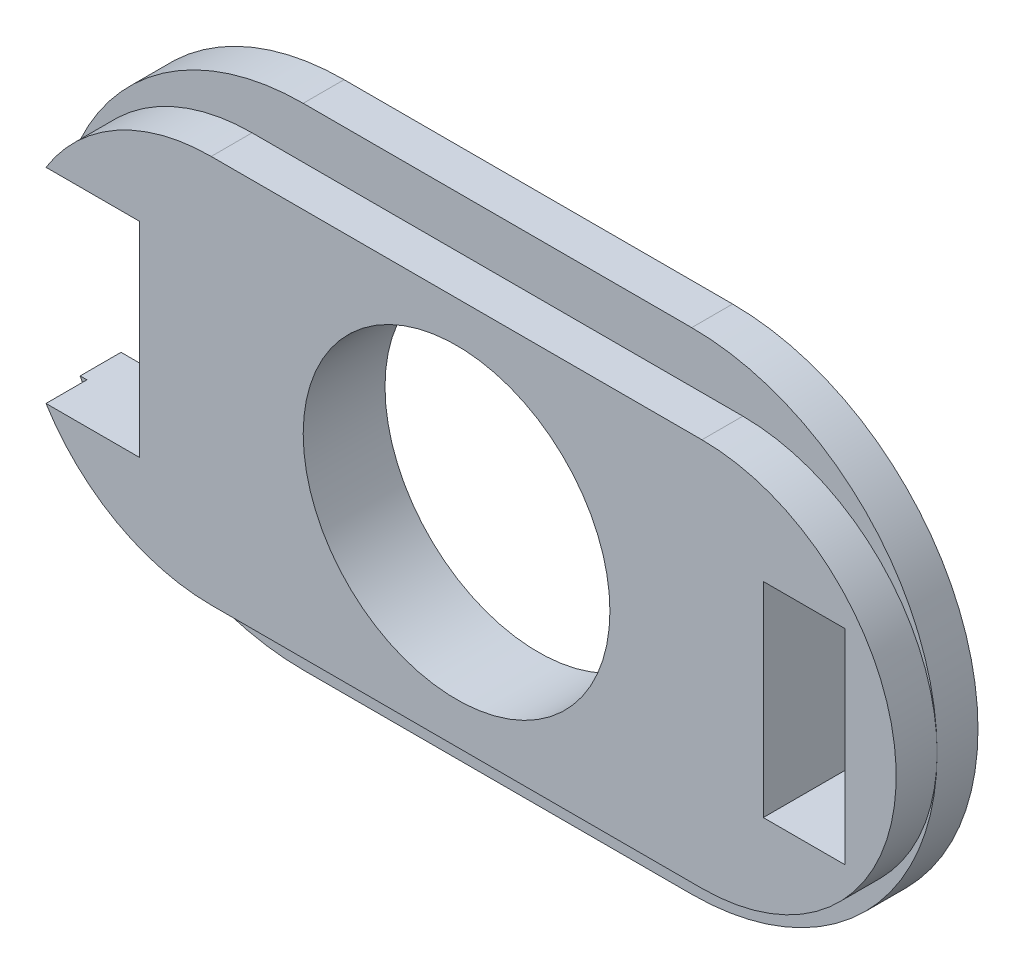
SolidWorks part; units mm, degrees
ref_plane "Face" through (0, 0, 0) normal (0, 0, 1) x (1, 0, 0)
ref_plane "Dessus" through (0, 0, 0) normal (0, 1, 0) x (1, 0, 0)
ref_plane "Droite" through (0, 0, 0) normal (1, 0, 0) x (0, 0, -1)
sketch "Esquisse1" plane through (0, 0, 0) normal (0, 0, 1) x (1, 0, 0)
  line L0 (-57.0491, 33.907) -> (-38.0491, 33.907)
  line L2 (-38.0491, 9.907) -> (-57.0491, 9.907)
  arc A0 (-38.0491, 9.907) -> (-38.0491, 33.907) centre (-38.0491, 21.907) ccw
  arc A1 (-57.0491, 33.907) -> (-57.0491, 9.907) centre (-57.0491, 21.907) ccw
extrude "Extrusion1" add sketch "Esquisse1" along normal blind 2
sketch "Esquisse2" plane through (0, 0, 2) normal (0, 0, 1) x (1, 0, 0)
  line L0 (-59.5491, 31.407) -> (-35.5491, 31.407)
  line L2 (-35.5491, 12.407) -> (-59.5491, 12.407)
  line L4 (-38.0491, 33.907) -> (-57.0491, 33.907) construction
  arc A0 (-35.5491, 12.407) -> (-35.5491, 31.407) centre (-35.5491, 21.907) ccw
  arc A1 (-59.5491, 31.407) -> (-59.5491, 12.407) centre (-59.5491, 21.907) ccw
  arc A2 (-57.0491, 33.907) -> (-57.0491, 9.907) centre (-57.0491, 21.907) ccw construction
  arc A3 (-38.0491, 9.907) -> (-38.0491, 33.907) centre (-38.0491, 21.907) ccw construction
  dimension "D1" = 19
  dimension "D2" = 2.5
extrude "Extrusion4" add sketch "Esquisse2" along normal blind 2
sketch "Esquisse3" plane through (0, 0, 4) normal (0, 0, 1) x (1, 0, 0)
  line L0 (-32.5491, 26.907) -> (-28.5491, 26.907)
  line L1 (-28.5491, 26.907) -> (-28.5491, 16.907)
  line L2 (-28.5491, 16.907) -> (-32.5491, 16.907)
  line L3 (-32.5491, 16.907) -> (-32.5491, 26.907)
  line L4 (-69.0491, 26.907) -> (-63.0491, 26.907)
  line L5 (-63.0491, 26.907) -> (-63.0491, 16.907)
  line L6 (-63.0491, 16.907) -> (-69.0491, 16.907)
  line L7 (-69.0491, 16.907) -> (-69.0491, 26.907)
  line L8 (-59.5491, 31.407) -> (-35.5491, 31.407) construction
  circle A0 centre (-47.5491, 21.907) radius 7.5
  arc A2 (-57.0491, 33.907) -> (-57.0491, 9.907) centre (-57.0491, 21.907) ccw construction
  dimension "D7" = 15
  dimension "D1" = 4
  dimension "D2" = 10
  dimension "D3" = 5
  dimension "D4" = 7
  dimension "D5" = 9.5
  dimension "D6" = 9.5
  dimension "D8" = 6
  dimension "D9" = 10
  dimension "D10" = 5
extrude "Enlèv. mat.-Extru.1" cut sketch "Esquisse3" against normal through all
